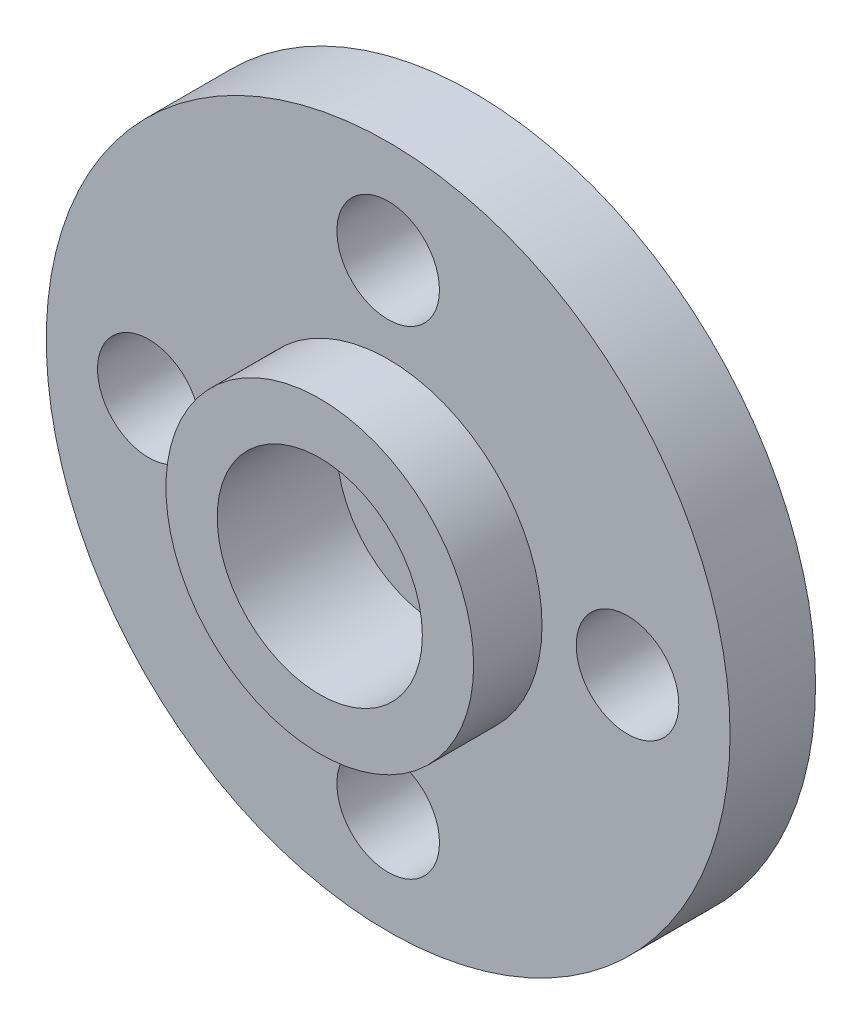
SolidWorks part; units mm, degrees
ref_plane "前视基准面" through (0, 0, 0) normal (0, 0, 1) x (1, 0, 0)
ref_plane "上视基准面" through (0, 0, 0) normal (0, 1, 0) x (1, 0, 0)
ref_plane "右视基准面" through (0, 0, 0) normal (1, 0, 0) x (0, 0, -1)
sketch "草图1" plane through (0, 0, 0) normal (0, 0, 1) x (1, 0, 0)
  circle A0 centre (0, 0) radius 10
  circle A1 centre (0, 7) radius 1.5
  circle A2 centre (0, -7) radius 1.5
  circle A3 centre (-7, 0) radius 1.5
  circle A4 centre (7, 0) radius 1.5
  point P11 (0, 0)
  point P12 (0, 0)
  dimension "D1" = 20
  dimension "D6" = 3
  dimension "D7" = 3
  dimension "D8" = 3
  dimension "D9" = 3
  dimension "D2" = 7
  dimension "D3" = 7
  dimension "D4" = 7
  dimension "D5" = 7
extrude "凸台-拉伸1" add sketch "草图1" along normal blind 2.5
sketch "草图2" plane through (0, 0, 2.5) normal (0, 0, 1) x (1, 0, 0)
  circle A0 centre (0, 0) radius 4.5
  dimension "D1" = 9
extrude "凸台-拉伸2" add sketch "草图2" along normal blind 2
sketch "草图3" plane through (0, 0, 4.5) normal (0, 0, 1) x (1, 0, 0)
  circle A0 centre (0, 0) radius 3
  dimension "D1" = 6
extrude "切除-拉伸1" cut sketch "草图3" against normal blind 3.5
sketch "草图4" plane through (0, 0, 1) normal (0, 0, 1) x (1, 0, 0)
  circle A0 centre (0, 0) radius 1.5
  dimension "D1" = 3
extrude "切除-拉伸2" cut sketch "草图4" against normal blind 3.5
